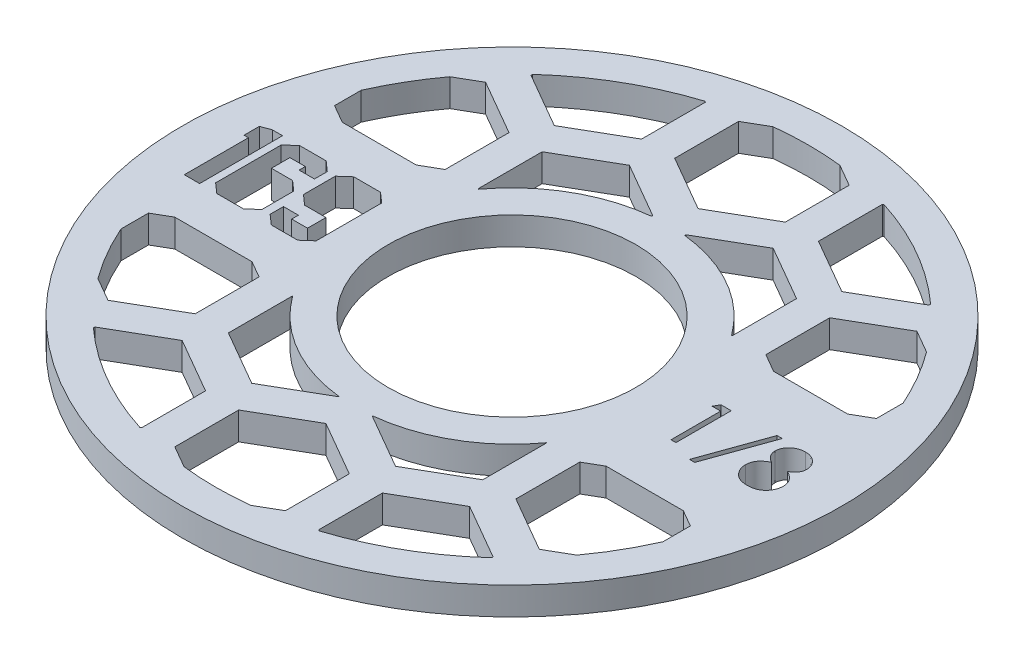
SolidWorks part; units mm, degrees
ref_plane "Front Plane" through (0, 0, 0) normal (0, 0, 1) x (1, 0, 0)
ref_plane "Top Plane" through (0, 0, 0) normal (0, 1, 0) x (1, 0, 0)
ref_plane "Right Plane" through (0, 0, 0) normal (1, 0, 0) x (0, 0, -1)
sketch "Sketch1" plane through (0, 0, 0) normal (0, 1, 0) x (1, 0, 0)
  circle A0 centre (0, 0) radius 14.224
  circle A1 centre (0, 0) radius 37.846
  dimension "D1" = 28.448
  dimension "D2" = 75.692
extrude "Boss-Extrude1" add sketch "Sketch1" along normal blind 3.175
sketch "Sketch2" plane through (0, 3.175, 0) normal (0, 1, 0) x (1, 0, 0)
  line L0 (-14.224, 0) -> (-37.846, 0) construction
  line L1 (-14.224, -4.7625) -> (-37.846, -4.7625) construction
  line L2 (14.224, 0) -> (37.846, 0) construction
  line L3 (14.224, -3.175) -> (37.846, -3.175) construction
  circle A0 centre (0, 0) radius 14.224 construction
  circle A1 centre (0, 0) radius 37.846 construction
  text T0 "169" font "Jersey M54" height 9.525
  text T1 "1/8" font "Century Gothic" height 6.35
  dimension "D1" = 4.7625
  dimension "D2" = 3.175
extrude "Cut-Extrude1" cut sketch "Sketch2" against normal through all both and the other way through all
sketch "Sketch3" plane through (0, 3.175, 0) normal (0, 1, 0) x (1, 0, 0)
  line L0 (0, -9.525) -> (0, 9.525)
  line L1 (36.6278, 9.525) -> (-36.6278, 9.525)
  line L2 (36.6278, -9.525) -> (-36.6278, -9.525)
  line L3 (16.51, -7.3323) -> (22.86, -3.6662)
  line L4 (0, -7.3323) -> (6.35, -3.6662)
  line L5 (6.35, -3.6662) -> (6.35, 3.6662)
  line L6 (6.35, 3.6662) -> (0, 7.3323)
  line L7 (0, 7.3323) -> (-6.35, 3.6662)
  line L8 (-6.35, 3.6662) -> (-6.35, -3.6662)
  line L9 (-6.35, -3.6662) -> (0, -7.3323)
  line L10 (8.255, -21.6304) -> (14.605, -17.9643)
  line L11 (14.605, -17.9643) -> (14.605, -10.6319)
  line L12 (14.605, -10.6319) -> (8.255, -6.9657)
  line L13 (8.255, -6.9657) -> (1.905, -10.6319)
  line L14 (1.905, -10.6319) -> (1.905, -17.9643)
  line L15 (1.905, -17.9643) -> (8.255, -21.6304)
  line L16 (22.86, -3.6662) -> (22.86, 3.6662)
  line L17 (22.86, 3.6662) -> (16.51, 7.3323)
  line L18 (16.51, 7.3323) -> (10.16, 3.6662)
  line L19 (10.16, 3.6662) -> (10.16, -3.6662)
  line L20 (10.16, -3.6662) -> (16.51, -7.3323)
  line L21 (24.765, -21.6304) -> (31.115, -17.9643)
  line L22 (31.115, -17.9643) -> (31.115, -10.6319)
  line L23 (31.115, -10.6319) -> (24.765, -6.9657)
  line L24 (24.765, -6.9657) -> (18.415, -10.6319)
  line L25 (18.415, -10.6319) -> (18.415, -17.9643)
  line L26 (18.415, -17.9643) -> (24.765, -21.6304)
  line L27 (33.02, -7.3323) -> (39.37, -3.6662)
  line L28 (39.37, -3.6662) -> (39.37, 3.6662)
  line L29 (39.37, 3.6662) -> (33.02, 7.3323)
  line L30 (33.02, 7.3323) -> (26.67, 3.6662)
  line L31 (26.67, 3.6662) -> (26.67, -3.6662)
  line L32 (26.67, -3.6662) -> (33.02, -7.3323)
  line L33 (41.275, -21.6304) -> (47.625, -17.9643)
  line L34 (47.625, -17.9643) -> (47.625, -10.6319)
  line L35 (47.625, -10.6319) -> (41.275, -6.9657)
  line L36 (41.275, -6.9657) -> (34.925, -10.6319)
  line L37 (34.925, -10.6319) -> (34.925, -17.9643)
  line L38 (34.925, -17.9643) -> (41.275, -21.6304)
  line L39 (-16.51, -7.3323) -> (-10.16, -3.6662)
  line L40 (-10.16, -3.6662) -> (-10.16, 3.6662)
  line L41 (-10.16, 3.6662) -> (-16.51, 7.3323)
  line L42 (-16.51, 7.3323) -> (-22.86, 3.6662)
  line L43 (-22.86, 3.6662) -> (-22.86, -3.6662)
  line L44 (-22.86, -3.6662) -> (-16.51, -7.3323)
  line L45 (-8.255, -21.6304) -> (-1.905, -17.9643)
  line L46 (-1.905, -17.9643) -> (-1.905, -10.6319)
  line L47 (-1.905, -10.6319) -> (-8.255, -6.9657)
  line L48 (-8.255, -6.9657) -> (-14.605, -10.6319)
  line L49 (-14.605, -10.6319) -> (-14.605, -17.9643)
  line L50 (-14.605, -17.9643) -> (-8.255, -21.6304)
  line L51 (-33.02, -7.3323) -> (-26.67, -3.6662)
  line L52 (-26.67, -3.6662) -> (-26.67, 3.6662)
  line L53 (-26.67, 3.6662) -> (-33.02, 7.3323)
  line L54 (-33.02, 7.3323) -> (-39.37, 3.6662)
  line L55 (-39.37, 3.6662) -> (-39.37, -3.6662)
  line L56 (-39.37, -3.6662) -> (-33.02, -7.3323)
  line L57 (-24.765, -21.6304) -> (-18.415, -17.9643)
  line L58 (-18.415, -17.9643) -> (-18.415, -10.6319)
  line L59 (-18.415, -10.6319) -> (-24.765, -6.9657)
  line L60 (-24.765, -6.9657) -> (-31.115, -10.6319)
  line L61 (-31.115, -10.6319) -> (-31.115, -17.9643)
  line L62 (-31.115, -17.9643) -> (-24.765, -21.6304)
  line L63 (0, 21.3697) -> (6.35, 25.0358)
  line L64 (6.35, 25.0358) -> (6.35, 32.3682)
  line L65 (6.35, 32.3682) -> (0, 36.0343)
  line L66 (0, 36.0343) -> (-6.35, 32.3682)
  line L67 (-6.35, 32.3682) -> (-6.35, 25.0358)
  line L68 (-6.35, 25.0358) -> (0, 21.3697)
  line L69 (8.255, 7.0716) -> (14.605, 10.7377)
  line L70 (14.605, 10.7377) -> (14.605, 18.0701)
  line L71 (14.605, 18.0701) -> (8.255, 21.7363)
  line L72 (8.255, 21.7363) -> (1.905, 18.0701)
  line L73 (1.905, 18.0701) -> (1.905, 10.7377)
  line L74 (1.905, 10.7377) -> (8.255, 7.0716)
  line L75 (-33.02, 21.3697) -> (-26.67, 25.0358)
  line L76 (-26.67, 25.0358) -> (-26.67, 32.3682)
  line L77 (-26.67, 32.3682) -> (-33.02, 36.0343)
  line L78 (-33.02, 36.0343) -> (-39.37, 32.3682)
  line L79 (-39.37, 32.3682) -> (-39.37, 25.0358)
  line L80 (-39.37, 25.0358) -> (-33.02, 21.3697)
  line L81 (-24.765, 7.0716) -> (-18.415, 10.7377)
  line L82 (-18.415, 10.7377) -> (-18.415, 18.0701)
  line L83 (-18.415, 18.0701) -> (-24.765, 21.7363)
  line L84 (-24.765, 21.7363) -> (-31.115, 18.0701)
  line L85 (-31.115, 18.0701) -> (-31.115, 10.7377)
  line L86 (-31.115, 10.7377) -> (-24.765, 7.0716)
  line L87 (-16.51, 21.3697) -> (-10.16, 25.0358)
  line L88 (-10.16, 25.0358) -> (-10.16, 32.3682)
  line L89 (-10.16, 32.3682) -> (-16.51, 36.0343)
  line L90 (-16.51, 36.0343) -> (-22.86, 32.3682)
  line L91 (-22.86, 32.3682) -> (-22.86, 25.0358)
  line L92 (-22.86, 25.0358) -> (-16.51, 21.3697)
  line L93 (-8.255, 7.0716) -> (-1.905, 10.7377)
  line L94 (-1.905, 10.7377) -> (-1.905, 18.0701)
  line L95 (-1.905, 18.0701) -> (-8.255, 21.7363)
  line L96 (-8.255, 21.7363) -> (-14.605, 18.0701)
  line L97 (-14.605, 18.0701) -> (-14.605, 10.7377)
  line L98 (-14.605, 10.7377) -> (-8.255, 7.0716)
  line L99 (16.51, 21.3697) -> (22.86, 25.0358)
  line L100 (22.86, 25.0358) -> (22.86, 32.3682)
  line L101 (22.86, 32.3682) -> (16.51, 36.0343)
  line L102 (16.51, 36.0343) -> (10.16, 32.3682)
  line L103 (10.16, 32.3682) -> (10.16, 25.0358)
  line L104 (10.16, 25.0358) -> (16.51, 21.3697)
  line L105 (24.765, 7.0716) -> (31.115, 10.7377)
  line L106 (31.115, 10.7377) -> (31.115, 18.0701)
  line L107 (31.115, 18.0701) -> (24.765, 21.7363)
  line L108 (24.765, 21.7363) -> (18.415, 18.0701)
  line L109 (18.415, 18.0701) -> (18.415, 10.7377)
  line L110 (18.415, 10.7377) -> (24.765, 7.0716)
  line L111 (33.02, 21.3697) -> (39.37, 25.0358)
  line L112 (39.37, 25.0358) -> (39.37, 32.3682)
  line L113 (39.37, 32.3682) -> (33.02, 36.0343)
  line L114 (33.02, 36.0343) -> (26.67, 32.3682)
  line L115 (26.67, 32.3682) -> (26.67, 25.0358)
  line L116 (26.67, 25.0358) -> (33.02, 21.3697)
  line L117 (41.275, 7.0716) -> (47.625, 10.7377)
  line L118 (47.625, 10.7377) -> (47.625, 18.0701)
  line L119 (47.625, 18.0701) -> (41.275, 21.7363)
  line L120 (41.275, 21.7363) -> (34.925, 18.0701)
  line L121 (34.925, 18.0701) -> (34.925, 10.7377)
  line L122 (34.925, 10.7377) -> (41.275, 7.0716)
  line L123 (0, -36.0343) -> (6.35, -32.3682)
  line L124 (6.35, -32.3682) -> (6.35, -25.0358)
  line L125 (6.35, -25.0358) -> (0, -21.3697)
  line L126 (0, -21.3697) -> (-6.35, -25.0358)
  line L127 (-6.35, -25.0358) -> (-6.35, -32.3682)
  line L128 (-6.35, -32.3682) -> (0, -36.0343)
  line L129 (8.255, -50.3324) -> (14.605, -46.6663)
  line L130 (14.605, -46.6663) -> (14.605, -39.3339)
  line L131 (14.605, -39.3339) -> (8.255, -35.6677)
  line L132 (8.255, -35.6677) -> (1.905, -39.3339)
  line L133 (1.905, -39.3339) -> (1.905, -46.6663)
  line L134 (1.905, -46.6663) -> (8.255, -50.3324)
  line L135 (-33.02, -36.0343) -> (-26.67, -32.3682)
  line L136 (-26.67, -32.3682) -> (-26.67, -25.0358)
  line L137 (-26.67, -25.0358) -> (-33.02, -21.3697)
  line L138 (-33.02, -21.3697) -> (-39.37, -25.0358)
  line L139 (-39.37, -25.0358) -> (-39.37, -32.3682)
  line L140 (-39.37, -32.3682) -> (-33.02, -36.0343)
  line L141 (-24.765, -50.3324) -> (-18.415, -46.6663)
  line L142 (-18.415, -46.6663) -> (-18.415, -39.3339)
  line L143 (-18.415, -39.3339) -> (-24.765, -35.6677)
  line L144 (-24.765, -35.6677) -> (-31.115, -39.3339)
  line L145 (-31.115, -39.3339) -> (-31.115, -46.6663)
  line L146 (-31.115, -46.6663) -> (-24.765, -50.3324)
  line L147 (-16.51, -36.0343) -> (-10.16, -32.3682)
  line L148 (-10.16, -32.3682) -> (-10.16, -25.0358)
  line L149 (-10.16, -25.0358) -> (-16.51, -21.3697)
  line L150 (-16.51, -21.3697) -> (-22.86, -25.0358)
  line L151 (-22.86, -25.0358) -> (-22.86, -32.3682)
  line L152 (-22.86, -32.3682) -> (-16.51, -36.0343)
  line L153 (-8.255, -50.3324) -> (-1.905, -46.6663)
  line L154 (-1.905, -46.6663) -> (-1.905, -39.3339)
  line L155 (-1.905, -39.3339) -> (-8.255, -35.6677)
  line L156 (-8.255, -35.6677) -> (-14.605, -39.3339)
  line L157 (-14.605, -39.3339) -> (-14.605, -46.6663)
  line L158 (-14.605, -46.6663) -> (-8.255, -50.3324)
  line L159 (16.51, -36.0343) -> (22.86, -32.3682)
  line L160 (22.86, -32.3682) -> (22.86, -25.0358)
  line L161 (22.86, -25.0358) -> (16.51, -21.3697)
  line L162 (16.51, -21.3697) -> (10.16, -25.0358)
  line L163 (10.16, -25.0358) -> (10.16, -32.3682)
  line L164 (10.16, -32.3682) -> (16.51, -36.0343)
  line L165 (24.765, -50.3324) -> (31.115, -46.6663)
  line L166 (31.115, -46.6663) -> (31.115, -39.3339)
  line L167 (31.115, -39.3339) -> (24.765, -35.6677)
  line L168 (24.765, -35.6677) -> (18.415, -39.3339)
  line L169 (18.415, -39.3339) -> (18.415, -46.6663)
  line L170 (18.415, -46.6663) -> (24.765, -50.3324)
  line L171 (33.02, -36.0343) -> (39.37, -32.3682)
  line L172 (39.37, -32.3682) -> (39.37, -25.0358)
  line L173 (39.37, -25.0358) -> (33.02, -21.3697)
  line L174 (33.02, -21.3697) -> (26.67, -25.0358)
  line L175 (26.67, -25.0358) -> (26.67, -32.3682)
  line L176 (26.67, -32.3682) -> (33.02, -36.0343)
  line L177 (41.275, -50.3324) -> (47.625, -46.6663)
  line L178 (47.625, -46.6663) -> (47.625, -39.3339)
  line L179 (47.625, -39.3339) -> (41.275, -35.6677)
  line L180 (41.275, -35.6677) -> (34.925, -39.3339)
  line L181 (34.925, -39.3339) -> (34.925, -46.6663)
  line L182 (34.925, -46.6663) -> (41.275, -50.3324)
  circle A0 centre (0, 0) radius 37.846 construction
  circle A1 centre (0, 0) radius 34.036
  circle A2 centre (0, 0) radius 18.034
  circle A3 centre (0, 0) radius 6.35 construction
  circle A4 centre (8.255, -14.2981) radius 6.35 construction
  point P4 (0, 0)
  point P10 (0, 9.525)
  point P13 (0, -9.525)
  dimension "D2" = 68.072
  dimension "D3" = 36.068
  dimension "D1" = 19.05
  dimension "D4" = 12.7
  dimension "D5" = 12.7
  dimension "D6" = 3.81
  dimension "D7" = 1.905
  dimension "D8" = 3
  dimension "D9" = 3
  dimension "D10" = 2
  dimension "D11" = 2
extrude "Cut-Extrude2" cut sketch "Sketch3" against normal through all both and the other way through all contours L84 A1 L85 L86 L1 L81 L82 L83 | L89 A1 L91 L92 L87 L88 | A2 L94 L95 L96 L97 L98 | L65 A1 L66 L67 L68 L63 L64 | A2 L69 L70 L71 L72 L73 | L100 A1 L102 L103 L104 L99 | L106 A1 L107 L108 L109 L110 L1 L105 | L21 A1 L22 L23 L2 L24 L25 L26 | A2 L14 L15 L10 L11 L12 | L164 A1 L160 L161 L162 L163 | L128 A1 L123 L124 L125 L126 L127 | A2 L48 L49 L50 L45 L46 | L151 A1 L147 L148 L149 L150 | L61 A1 L62 L57 L58 L59 L2 L60
